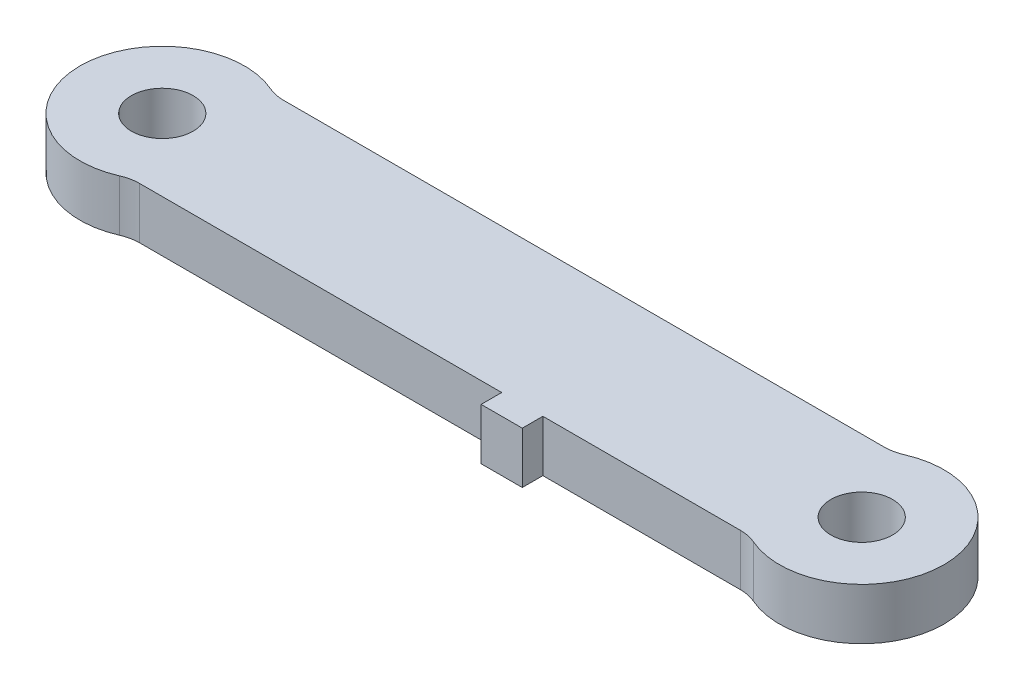
SolidWorks part; units mm, degrees
ref_plane "Front Plane" through (0, 0, 0) normal (0, 0, 1) x (1, 0, 0)
ref_plane "Top Plane" through (0, 0, 0) normal (0, 1, 0) x (1, 0, 0)
ref_plane "Right Plane" through (0, 0, 0) normal (1, 0, 0) x (0, 0, -1)
sketch "Sketch1" plane through (0, 0, 0) normal (0, 1, 0) x (1, 0, 0)
  line L0 (2.4593, 4.445) -> (40.7207, 4.445)
  line L1 (2.4593, -4.445) -> (40.7207, -4.445)
  circle A0 centre (0, 0) radius 1.905
  circle A1 centre (0, 0) radius 5.08
  circle A2 centre (43.18, 0) radius 1.905
  circle A3 centre (43.18, 0) radius 5.08
  dimension "D1" = 3.81
  dimension "D2" = 10.16
  dimension "D5" = 3.81
  dimension "D6" = 10.16
  dimension "D3" = 8.89
  dimension "D4" = 4.445
  dimension "D7" = 0
  dimension "D8" = 5.08
  dimension "D9" = 4.445
  dimension "D10" = 43.18
extrude "Boss-Extrude1" add sketch "Sketch1" along normal blind 3.175 contours A1 A0 | A3 L0 A1 L1 | A3 A2
fillet "Fillet1" radius 2.54 4 edges at (2.4593, 1.5875, 4.445) (2.4593, 1.5875, -4.445) (40.7207, 1.5875, -4.445) (40.7207, 1.5875, 4.445)
sketch "Sketch2" plane through (0, 0, 4.445) normal (0, 0, 1) x (1, 0, 0)
  line L0 (3.0454, 3.175) -> (40.1346, 3.175) construction
  line L1 (25.4, 3.175) -> (27.94, 3.175)
  line L2 (25.4, 3.175) -> (25.4, 0)
  line L3 (25.4, 0) -> (27.94, 0)
  line L4 (27.94, 3.175) -> (27.94, 0)
  line L5 (3.0454, 0) -> (40.1346, 0) construction
  dimension "D1" = 2.54
  dimension "D2" = 25.4
extrude "Boss-Extrude2" add sketch "Sketch2" along normal blind 1.27
